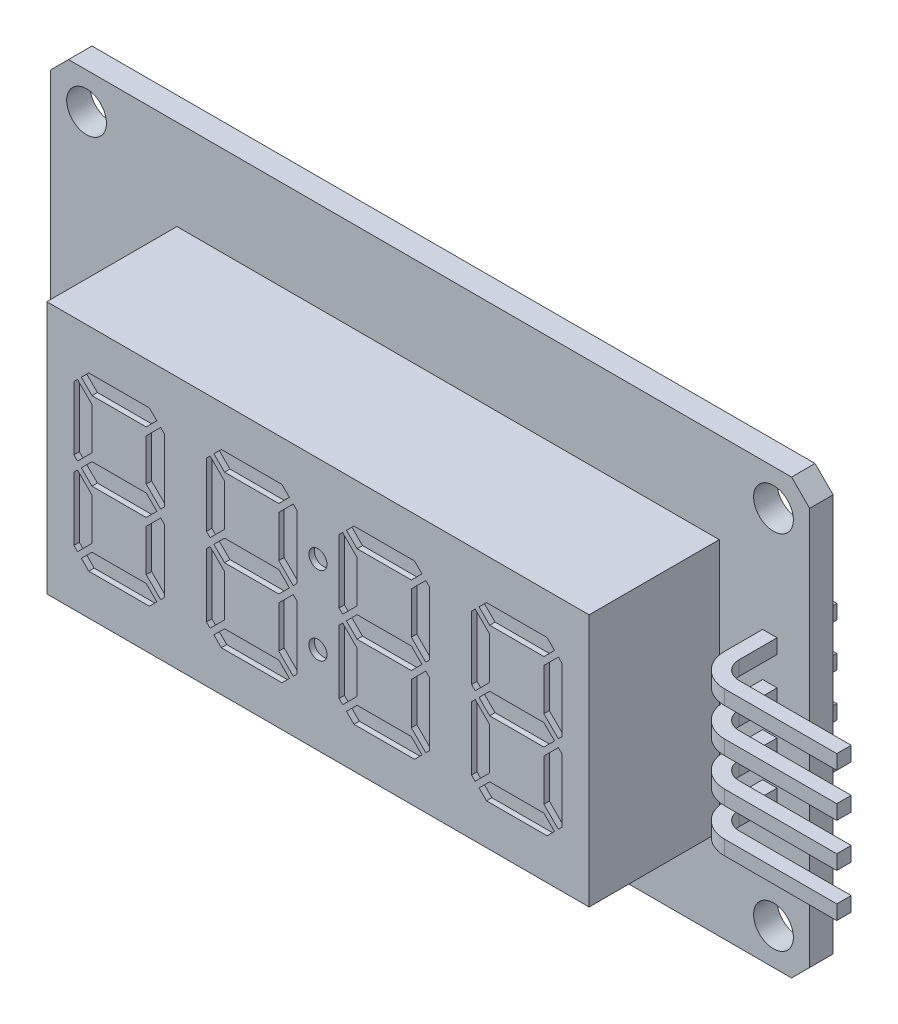
SolidWorks part; units mm, degrees
ref_plane "Спереди" through (0, 0, 0) normal (0, 0, 1) x (1, 0, 0)
ref_plane "Сверху" through (0, 0, 0) normal (0, 1, 0) x (1, 0, 0)
ref_plane "Справа" through (0, 0, 0) normal (1, 0, 0) x (0, 0, -1)
sketch "Эскиз1" plane through (0, 0, 0) normal (0, 0, 1) x (1, 0, 0)
  line L0 (0, 0) -> (0, 16.9884) construction
  line L1 (20, -12) -> (-20, -12)
  line L2 (21, -11) -> (21, 11)
  line L3 (20, 12) -> (-20, 12)
  line L4 (-21, -11) -> (-21, 11)
  line L5 (21, -12) -> (-21, 12) construction
  line L6 (21, 12) -> (-21, -12) construction
  line L7 (0, 0) -> (25.1525, 0) construction
  line L8 (-20, 12) -> (-21, 11)
  line L9 (19, -10) -> (-19, -10) construction
  line L10 (19, -10) -> (19, 10) construction
  line L11 (19, 10) -> (-19, 10) construction
  line L12 (-19, -10) -> (-19, 10) construction
  line L13 (19, -10) -> (-19, 10) construction
  line L14 (19, 10) -> (-19, -10) construction
  line L15 (21, 11) -> (20, 12)
  line L16 (21, -11) -> (20, -12)
  line L17 (-20, -12) -> (-21, -11)
  circle A0 centre (-19, 10) radius 1.1
  circle A1 centre (19, 10) radius 1.1
  circle A2 centre (19, -10) radius 1.1
  circle A3 centre (-19, -10) radius 1.1
  point P0 (0, 0)
  dimension "D3" = 2.2
  dimension "D4" = 22.2
  dimension "D5" = 40.2
  dimension "D1" = 42
  dimension "D2" = 24
extrude "Бобышка-Вытянуть1" add sketch "Эскиз1" along normal blind 1.3
sketch "Эскиз2" plane through (0, 0, 1.3) normal (0, 0, 1) x (1, 0, 0)
  line L0 (0, 0) -> (15.7392, 0) construction
  line L1 (-21, 11) -> (-21, -11) construction
  line L2 (16, -7) -> (-14, -7)
  line L3 (16, -7) -> (16, 7)
  line L4 (16, 7) -> (-14, 7)
  line L5 (-14, -7) -> (-14, 7)
  line L6 (16, -7) -> (-14, 7) construction
  line L7 (16, 7) -> (-14, -7) construction
  point P3 (1, 0)
  dimension "D1" = 14
  dimension "D2" = 30
  dimension "D3" = 7
extrude "Бобышка-Вытянуть2" add sketch "Эскиз2" along normal blind 7.2
sketch "Эскиз3" plane through (0, 0, 0) normal (0, 0, -1) x (-1, 0, 0)
  line L0 (0, 0) -> (23.0936, 0) construction
  line L1 (21, 11) -> (21, -11) construction
  line L2 (16.7, -6.5) -> (8.7, -6.5)
  line L3 (16.7, -6.5) -> (16.7, 6.5)
  line L4 (16.7, 6.5) -> (8.7, 6.5)
  line L5 (8.7, -6.5) -> (8.7, 6.5)
  line L6 (16.7, -6.5) -> (8.7, 6.5) construction
  line L7 (16.7, 6.5) -> (8.7, -6.5) construction
  point P3 (12.7, 0)
  dimension "D1" = 13
  dimension "D2" = 8
  dimension "D3" = 4.3
extrude "Бобышка-Вытянуть3" add sketch "Эскиз3" along normal blind 2.5
ref_plane "Плоскость1" through (0, 3.5, 0) normal (0, 1, 0) x (1, 0, 0)
sketch "Эскиз4" plane through (0, 3.5, 0) normal (0, 1, 0) x (1, 0, 0)
  line L0 (18.4, 2) -> (18.4, -3.4)
  line L1 (20.2, -5.2) -> (26.4, -5.2)
  line L2 (26.4, -5.2) -> (26.4, -4.4)
  line L3 (26.4, -4.4) -> (20.2, -4.4)
  line L4 (19.2, -3.4) -> (19.2, 2)
  line L5 (19.2, 2) -> (18.4, 2)
  line L6 (-20, 0) -> (20, 0) construction
  line L7 (21, -1.3) -> (21, 0) construction
  arc A0 (20.2, -4.4) -> (19.2, -3.4) centre (20.2, -3.4) cw
  arc A1 (18.4, -3.4) -> (20.2, -5.2) centre (20.2, -3.4) ccw
  dimension "D2" = 1
  dimension "D3" = 1.8
  dimension "D1" = 0.8
  dimension "D4" = 2
  dimension "D5" = 7.2
  dimension "D6" = 8
  dimension "D7" = 1.8
extrude "Бобышка-Вытянуть4" add sketch "Эскиз4" along normal mid plane 0.8
pattern_linear "Линейный массив1" count 4 spacing 2.4 along (0, -1, 0) of "Бобышка-Вытянуть4"
sketch "Эскиз5" plane through (0, 0, 8.5) normal (0, 0, 1) x (1, 0, 0)
  line L0 (0, 0) -> (-17.4491, 0) construction
  line L1 (0, 0) -> (0, 10.4993) construction
  line L2 (-10, -4.3379) -> (-10, 4.3379) construction
  line L3 (-10, 0) -> (-10, -4.2496) construction
  line L4 (-8.5, 3.75) -> (-11.5, 3.75)
  line L5 (-11.5, 3.75) -> (-12.0879, 4.3379)
  line L6 (-11.6757, 4.75) -> (-8.3243, 4.75)
  line L7 (-8.5, 0.5879) -> (-11.5, 0.5879)
  line L8 (-11.5, 0.5879) -> (-12.0879, 0)
  line L9 (-12.0879, 0) -> (-11.5, -0.5879)
  line L10 (-11.5, -0.5879) -> (-8.5, -0.5879)
  line L11 (-7.2606, 2.1689) -> (-12.7394, 2.1689) construction
  line L12 (-11.5, 1.0121) -> (-11.5, 3.3257)
  line L13 (-11.5, 3.3257) -> (-12.3, 4.1257)
  line L14 (-12.5, 3.9257) -> (-12.5, 0.4121)
  line L15 (-11.5, 1.0121) -> (-12.3, 0.2121)
  line L16 (-12.0879, 4.3379) -> (-11.6757, 4.75)
  line L17 (-12.3, 4.1257) -> (-12.5, 3.9257)
  line L18 (-12.3, 0.2121) -> (-12.5, 0.4121)
  line L19 (-7.7, 0.2121) -> (-7.5, 0.4121)
  line L20 (-7.7, 4.1257) -> (-7.5, 3.9257)
  line L21 (-7.9121, 4.3379) -> (-8.3243, 4.75)
  line L22 (-8.5, 1.0121) -> (-7.7, 0.2121)
  line L23 (-7.5, 3.9257) -> (-7.5, 0.4121)
  line L24 (-8.5, 3.3257) -> (-7.7, 4.1257)
  line L25 (-8.5, 1.0121) -> (-8.5, 3.3257)
  line L26 (-7.9121, 0) -> (-8.5, -0.5879)
  line L27 (-8.5, 0.5879) -> (-7.9121, 0)
  line L28 (-8.5, 3.75) -> (-7.9121, 4.3379)
  line L29 (-7.2606, -2.1689) -> (-12.7394, -2.1689) construction
  line L30 (-8.5, -3.75) -> (-7.9121, -4.3379)
  line L31 (-8.5, -1.0121) -> (-8.5, -3.3257)
  line L32 (-8.5, -3.3257) -> (-7.7, -4.1257)
  line L33 (-7.5, -3.9257) -> (-7.5, -0.4121)
  line L34 (-8.5, -1.0121) -> (-7.7, -0.2121)
  line L35 (-7.9121, -4.3379) -> (-8.3243, -4.75)
  line L36 (-7.7, -4.1257) -> (-7.5, -3.9257)
  line L37 (-7.7, -0.2121) -> (-7.5, -0.4121)
  line L38 (-12.3, -0.2121) -> (-12.5, -0.4121)
  line L39 (-12.3, -4.1257) -> (-12.5, -3.9257)
  line L40 (-12.0879, -4.3379) -> (-11.6757, -4.75)
  line L41 (-11.5, -1.0121) -> (-12.3, -0.2121)
  line L42 (-12.5, -3.9257) -> (-12.5, -0.4121)
  line L43 (-11.5, -3.3257) -> (-12.3, -4.1257)
  line L44 (-11.5, -1.0121) -> (-11.5, -3.3257)
  line L45 (-11.6757, -4.75) -> (-8.3243, -4.75)
  line L46 (-11.5, -3.75) -> (-12.0879, -4.3379)
  line L47 (-8.5, -3.75) -> (-11.5, -3.75)
  line L48 (-1.1667, 3.75) -> (-4.1667, 3.75)
  line L49 (-4.1667, 3.75) -> (-4.7545, 4.3379)
  line L50 (-4.3424, 4.75) -> (-0.9909, 4.75)
  line L51 (-1.1667, 0.5879) -> (-4.1667, 0.5879)
  line L52 (-4.1667, 0.5879) -> (-4.7545, 0)
  line L53 (-4.7545, 0) -> (-4.1667, -0.5879)
  line L54 (-4.1667, -0.5879) -> (-1.1667, -0.5879)
  line L55 (-4.1667, 1.0121) -> (-4.1667, 3.3257)
  line L56 (-4.1667, 3.3257) -> (-4.9667, 4.1257)
  line L57 (-5.1667, 3.9257) -> (-5.1667, 0.4121)
  line L58 (-4.1667, 1.0121) -> (-4.9667, 0.2121)
  line L59 (-4.7545, 4.3379) -> (-4.3424, 4.75)
  line L60 (-4.9667, 4.1257) -> (-5.1667, 3.9257)
  line L61 (-4.9667, 0.2121) -> (-5.1667, 0.4121)
  line L62 (-0.3667, 0.2121) -> (-0.1667, 0.4121)
  line L63 (-0.3667, 4.1257) -> (-0.1667, 3.9257)
  line L64 (-0.5788, 4.3379) -> (-0.9909, 4.75)
  line L65 (-1.1667, 1.0121) -> (-0.3667, 0.2121)
  line L66 (-0.1667, 3.9257) -> (-0.1667, 0.4121)
  line L67 (-1.1667, 3.3257) -> (-0.3667, 4.1257)
  line L68 (-1.1667, 1.0121) -> (-1.1667, 3.3257)
  line L69 (-0.5788, 0) -> (-1.1667, -0.5879)
  line L70 (-1.1667, 0.5879) -> (-0.5788, 0)
  line L71 (-1.1667, 3.75) -> (-0.5788, 4.3379)
  line L72 (-1.1667, -3.75) -> (-0.5788, -4.3379)
  line L73 (-1.1667, -1.0121) -> (-1.1667, -3.3257)
  line L74 (-1.1667, -3.3257) -> (-0.3667, -4.1257)
  line L75 (-0.1667, -3.9257) -> (-0.1667, -0.4121)
  line L76 (-1.1667, -1.0121) -> (-0.3667, -0.2121)
  line L77 (-0.5788, -4.3379) -> (-0.9909, -4.75)
  line L78 (-0.3667, -4.1257) -> (-0.1667, -3.9257)
  line L79 (-0.3667, -0.2121) -> (-0.1667, -0.4121)
  line L80 (-4.9667, -0.2121) -> (-5.1667, -0.4121)
  line L81 (-4.9667, -4.1257) -> (-5.1667, -3.9257)
  line L82 (-4.7545, -4.3379) -> (-4.3424, -4.75)
  line L83 (-4.1667, -1.0121) -> (-4.9667, -0.2121)
  line L84 (-5.1667, -3.9257) -> (-5.1667, -0.4121)
  line L85 (-4.1667, -3.3257) -> (-4.9667, -4.1257)
  line L86 (-4.1667, -1.0121) -> (-4.1667, -3.3257)
  line L87 (-4.3424, -4.75) -> (-0.9909, -4.75)
  line L88 (-4.1667, -3.75) -> (-4.7545, -4.3379)
  line L89 (-1.1667, -3.75) -> (-4.1667, -3.75)
  line L90 (-2.6667, -4.3379) -> (-2.6667, 4.3379) construction
  line L91 (-2.6667, 0) -> (-2.6667, -4.2496) construction
  line L92 (0.0728, 2.1689) -> (-5.4061, 2.1689) construction
  line L93 (0.0728, -2.1689) -> (-5.4061, -2.1689) construction
  line L94 (6.1667, 3.75) -> (3.1667, 3.75)
  line L95 (3.1667, 3.75) -> (2.5788, 4.3379)
  line L96 (2.9909, 4.75) -> (6.3424, 4.75)
  line L97 (6.1667, 0.5879) -> (3.1667, 0.5879)
  line L98 (3.1667, 0.5879) -> (2.5788, 0)
  line L99 (2.5788, 0) -> (3.1667, -0.5879)
  line L100 (3.1667, -0.5879) -> (6.1667, -0.5879)
  line L101 (3.1667, 1.0121) -> (3.1667, 3.3257)
  line L102 (3.1667, 3.3257) -> (2.3667, 4.1257)
  line L103 (2.1667, 3.9257) -> (2.1667, 0.4121)
  line L104 (3.1667, 1.0121) -> (2.3667, 0.2121)
  line L105 (2.5788, 4.3379) -> (2.9909, 4.75)
  line L106 (2.3667, 4.1257) -> (2.1667, 3.9257)
  line L107 (2.3667, 0.2121) -> (2.1667, 0.4121)
  line L108 (6.9667, 0.2121) -> (7.1667, 0.4121)
  line L109 (6.9667, 4.1257) -> (7.1667, 3.9257)
  line L110 (6.7545, 4.3379) -> (6.3424, 4.75)
  line L111 (6.1667, 1.0121) -> (6.9667, 0.2121)
  line L112 (7.1667, 3.9257) -> (7.1667, 0.4121)
  line L113 (6.1667, 3.3257) -> (6.9667, 4.1257)
  line L114 (6.1667, 1.0121) -> (6.1667, 3.3257)
  line L115 (6.7545, 0) -> (6.1667, -0.5879)
  line L116 (6.1667, 0.5879) -> (6.7545, 0)
  line L117 (6.1667, 3.75) -> (6.7545, 4.3379)
  line L118 (6.1667, -3.75) -> (6.7545, -4.3379)
  line L119 (6.1667, -1.0121) -> (6.1667, -3.3257)
  line L120 (6.1667, -3.3257) -> (6.9667, -4.1257)
  line L121 (7.1667, -3.9257) -> (7.1667, -0.4121)
  line L122 (6.1667, -1.0121) -> (6.9667, -0.2121)
  line L123 (6.7545, -4.3379) -> (6.3424, -4.75)
  line L124 (6.9667, -4.1257) -> (7.1667, -3.9257)
  line L125 (6.9667, -0.2121) -> (7.1667, -0.4121)
  line L126 (2.3667, -0.2121) -> (2.1667, -0.4121)
  line L127 (2.3667, -4.1257) -> (2.1667, -3.9257)
  line L128 (2.5788, -4.3379) -> (2.9909, -4.75)
  line L129 (3.1667, -1.0121) -> (2.3667, -0.2121)
  line L130 (2.1667, -3.9257) -> (2.1667, -0.4121)
  line L131 (3.1667, -3.3257) -> (2.3667, -4.1257)
  line L132 (3.1667, -1.0121) -> (3.1667, -3.3257)
  line L133 (2.9909, -4.75) -> (6.3424, -4.75)
  line L134 (3.1667, -3.75) -> (2.5788, -4.3379)
  line L135 (6.1667, -3.75) -> (3.1667, -3.75)
  line L136 (4.6667, -4.3379) -> (4.6667, 4.3379) construction
  line L137 (4.6667, 0) -> (4.6667, -4.2496) construction
  line L138 (7.4061, 2.1689) -> (1.9272, 2.1689) construction
  line L139 (7.4061, -2.1689) -> (1.9272, -2.1689) construction
  line L140 (13.5, 3.75) -> (10.5, 3.75)
  line L141 (10.5, 3.75) -> (9.9121, 4.3379)
  line L142 (10.3243, 4.75) -> (13.6757, 4.75)
  line L143 (13.5, 0.5879) -> (10.5, 0.5879)
  line L144 (10.5, 0.5879) -> (9.9121, 0)
  line L145 (9.9121, 0) -> (10.5, -0.5879)
  line L146 (10.5, -0.5879) -> (13.5, -0.5879)
  line L147 (10.5, 1.0121) -> (10.5, 3.3257)
  line L148 (10.5, 3.3257) -> (9.7, 4.1257)
  line L149 (9.5, 3.9257) -> (9.5, 0.4121)
  line L150 (10.5, 1.0121) -> (9.7, 0.2121)
  line L151 (9.9121, 4.3379) -> (10.3243, 4.75)
  line L152 (9.7, 4.1257) -> (9.5, 3.9257)
  line L153 (9.7, 0.2121) -> (9.5, 0.4121)
  line L154 (14.3, 0.2121) -> (14.5, 0.4121)
  line L155 (14.3, 4.1257) -> (14.5, 3.9257)
  line L156 (14.0879, 4.3379) -> (13.6757, 4.75)
  line L157 (13.5, 1.0121) -> (14.3, 0.2121)
  line L158 (14.5, 3.9257) -> (14.5, 0.4121)
  line L159 (13.5, 3.3257) -> (14.3, 4.1257)
  line L160 (13.5, 1.0121) -> (13.5, 3.3257)
  line L161 (14.0879, 0) -> (13.5, -0.5879)
  line L162 (13.5, 0.5879) -> (14.0879, 0)
  line L163 (13.5, 3.75) -> (14.0879, 4.3379)
  line L164 (13.5, -3.75) -> (14.0879, -4.3379)
  line L165 (13.5, -1.0121) -> (13.5, -3.3257)
  line L166 (13.5, -3.3257) -> (14.3, -4.1257)
  line L167 (14.5, -3.9257) -> (14.5, -0.4121)
  line L168 (13.5, -1.0121) -> (14.3, -0.2121)
  line L169 (14.0879, -4.3379) -> (13.6757, -4.75)
  line L170 (14.3, -4.1257) -> (14.5, -3.9257)
  line L171 (14.3, -0.2121) -> (14.5, -0.4121)
  line L172 (9.7, -0.2121) -> (9.5, -0.4121)
  line L173 (9.7, -4.1257) -> (9.5, -3.9257)
  line L174 (9.9121, -4.3379) -> (10.3243, -4.75)
  line L175 (10.5, -1.0121) -> (9.7, -0.2121)
  line L176 (9.5, -3.9257) -> (9.5, -0.4121)
  line L177 (10.5, -3.3257) -> (9.7, -4.1257)
  line L178 (10.5, -1.0121) -> (10.5, -3.3257)
  line L179 (10.3243, -4.75) -> (13.6757, -4.75)
  line L180 (10.5, -3.75) -> (9.9121, -4.3379)
  line L181 (13.5, -3.75) -> (10.5, -3.75)
  line L182 (12, -4.3379) -> (12, 4.3379) construction
  line L183 (12, 0) -> (12, -4.2496) construction
  line L184 (14.7394, 2.1689) -> (9.2606, 2.1689) construction
  line L185 (14.7394, -2.1689) -> (9.2606, -2.1689) construction
  line L186 (16, -7) -> (16, 7) construction
  line L187 (-14, 7) -> (-14, -7) construction
  point P6 (-8.5, 2.1689)
  point P9 (-10, 4.75)
  point P23 (-12.5, 2.1689)
  point P24 (-11.5, 2.1689)
  point P28 (-1.1667, 2.1689)
  point P32 (-10, 2.1689)
  point P41 (-10, -0.5879)
  point P43 (-10, 0.5879)
  point P44 (-10, 3.75)
  point P45 (-7.5, 2.1689)
  point P67 (-7.5, -2.1689)
  point P68 (-10, -3.75)
  point P69 (-10, -2.1689)
  point P70 (-11.5, -2.1689)
  point P71 (-12.5, -2.1689)
  point P72 (-10, -4.75)
  point P73 (-8.5, -2.1689)
  point P76 (-2.6667, 4.75)
  point P89 (-5.1667, 2.1689)
  point P90 (-4.1667, 2.1689)
  point P96 (-2.6667, 2.1689)
  point P105 (-2.6667, -0.5879)
  point P107 (-2.6667, 0.5879)
  point P108 (-2.6667, 3.75)
  point P109 (-0.1667, 2.1689)
  point P131 (-0.1667, -2.1689)
  point P132 (-2.6667, -3.75)
  point P133 (-2.6667, -2.1689)
  point P134 (-4.1667, -2.1689)
  point P135 (-5.1667, -2.1689)
  point P136 (-2.6667, -4.75)
  point P137 (-1.1667, -2.1689)
  point P140 (6.1667, 2.1689)
  point P143 (4.6667, 4.75)
  point P155 (2.1667, 2.1689)
  point P156 (3.1667, 2.1689)
  point P162 (4.6667, 2.1689)
  point P171 (4.6667, -0.5879)
  point P173 (4.6667, 0.5879)
  point P174 (4.6667, 3.75)
  point P175 (7.1667, 2.1689)
  point P197 (7.1667, -2.1689)
  point P198 (4.6667, -3.75)
  point P199 (4.6667, -2.1689)
  point P200 (3.1667, -2.1689)
  point P201 (2.1667, -2.1689)
  point P202 (4.6667, -4.75)
  point P203 (6.1667, -2.1689)
  point P206 (13.5, 2.1689)
  point P209 (12, 4.75)
  point P221 (9.5, 2.1689)
  point P222 (10.5, 2.1689)
  point P228 (12, 2.1689)
  point P237 (12, -0.5879)
  point P239 (12, 0.5879)
  point P240 (12, 3.75)
  point P241 (14.5, 2.1689)
  point P263 (14.5, -2.1689)
  point P264 (12, -3.75)
  point P265 (12, -2.1689)
  point P266 (10.5, -2.1689)
  point P267 (9.5, -2.1689)
  point P268 (12, -4.75)
  point P269 (13.5, -2.1689)
  dimension "D1" = 45
  dimension "D2" = 4
  dimension "D3" = 45
  dimension "D4" = 0.3
  dimension "D5" = 5
  dimension "D6" = 9.5
  dimension "D7" = 1
  dimension "D8" = 1
  dimension "D9" = 0.2
  dimension "D10" = 0.3
  dimension "D11" = 1.5
  dimension "D12" = 1.5
extrude "Вырез-Вытянуть1" cut sketch "Эскиз5" against normal blind 0.3
sketch "Эскиз7" plane through (0, 0, 8.5) normal (0, 0, 1) x (1, 0, 0)
  line L0 (2.1667, -0.4121) -> (2.1667, -3.9257) construction
  line L1 (-0.1667, -2.1689) -> (2.1667, -2.1689) construction
  line L2 (-0.1667, -3.9257) -> (-0.1667, -0.4121) construction
  line L3 (-0.1667, 2.1689) -> (2.1667, 2.1689) construction
  line L4 (-0.1667, 0.4121) -> (-0.1667, 3.9257) construction
  line L5 (2.1667, 3.9257) -> (2.1667, 0.4121) construction
  circle A0 centre (1, 2.1689) radius 0.5
  circle A1 centre (1, -2.1689) radius 0.5
  dimension "D1" = 1
extrude "Вырез-Вытянуть2" cut sketch "Эскиз7" against normal blind 0.3
